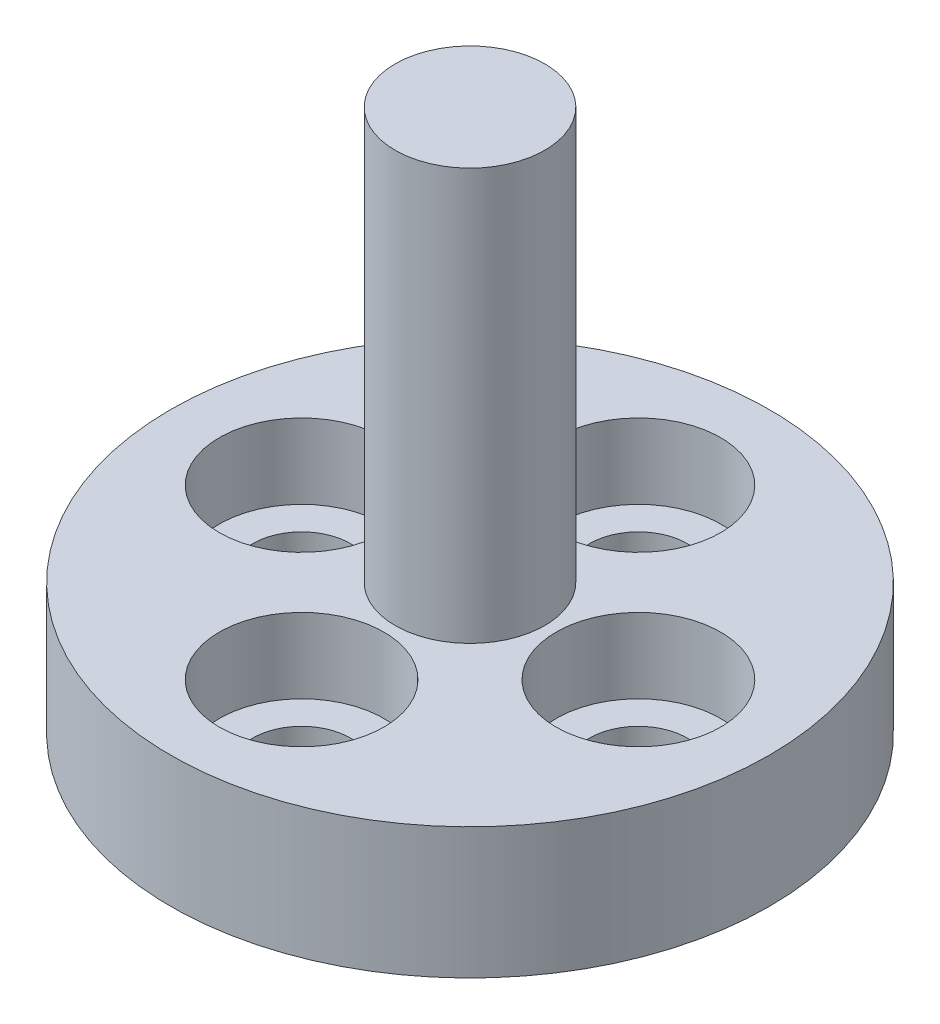
SolidWorks part; units mm, degrees
ref_plane "Front Plane" through (0, 0, 0) normal (0, 0, 1) x (1, 0, 0)
ref_plane "Top Plane" through (0, 0, 0) normal (0, 1, 0) x (1, 0, 0)
ref_plane "Right Plane" through (0, 0, 0) normal (1, 0, 0) x (0, 0, -1)
sketch "Sketch1" plane through (0, 0, 0) normal (0, 0, 1) x (1, 0, 0)
  line L0 (0, 0) -> (8, 0)
  line L1 (8, 0) -> (8, 3.5)
  line L2 (8, 3.5) -> (2, 3.5)
  line L3 (2, 3.5) -> (2, 14.5)
  line L4 (2, 14.5) -> (0, 14.5)
  line L5 (0, 14.5) -> (0, 0)
  dimension "D1" = 2
  dimension "D2" = 8
  dimension "D3" = 14.5
  dimension "D4" = 11
revolve "Revolve1" add sketch "Sketch1" angle 360 about L5
sketch "Sketch2" plane through (0, 3.5, 0) normal (0, 1, 0) x (1, 0, 0)
  line L0 (0, 0) -> (-4.5, 0) construction
  line L1 (-4.5, 0) -> (0, 4.5) construction
  line L2 (0, 4.5) -> (4.5, 0) construction
  line L3 (4.5, 0) -> (0, -4.5) construction
  line L4 (0, -4.5) -> (-4.5, 0) construction
  circle A0 centre (0, 0) radius 4.5
  dimension "D1" = 9
hole_wizard "CBORE for M2 SHCS1" positions "3DSketch2" profile "Sketch4" counterbore size "M2" standard "ANSI Metric"
sketch3d "3DSketch2"
  point P0 (-4.5, 3.5, 0)
  point P3 (0, 3.5, -4.5)
  point P6 (4.5, 3.5, 0)
  point P9 (0, 3.5, 4.5)
sketch "Sketch4" plane through (-4.5, 3.5, 0) normal (1, 0, 0) x (0, 0, 1)
  line L0 (0, 0) -> (0, 5.7811)
  line L1 (0, 5.7811) -> (1.3, 5)
  line L2 (1.3, 5) -> (1.3, 2)
  line L3 (1.3, 2) -> (2.2, 2)
  line L4 (2.2, 2) -> (2.2, 0)
  line L5 (2.2, 0) -> (0, 0)
  line L10 (0, 5.7811) -> (-1.3, 5) construction
  line L11 (0, -6.35) -> (0, 107.95) construction
  dimension "Hole Dia." = 2.6
  dimension "Hole Depth" = 5
  dimension "C'Bore Dia." = 4.4
  dimension "C'Bore Depth" = 2
  dimension "Drill Angle" = 118
